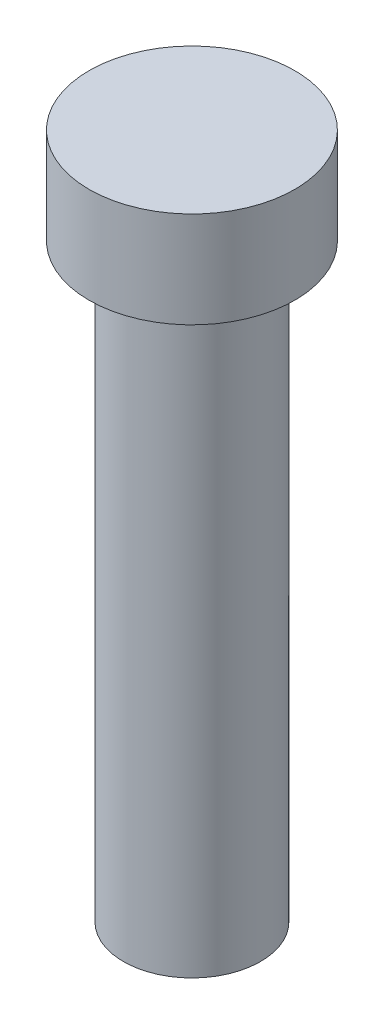
SolidWorks part; units mm, degrees
ref_plane "Front Plane" through (0, 0, 0) normal (0, 0, 1) x (1, 0, 0)
ref_plane "Top Plane" through (0, 0, 0) normal (0, 1, 0) x (1, 0, 0)
ref_plane "Right Plane" through (0, 0, 0) normal (1, 0, 0) x (0, 0, -1)
sketch "Sketch1" plane through (0, 0, 0) normal (0, 1, 0) x (1, 0, 0)
  circle A0 centre (0, 0) radius 7.5
  dimension "D1" = 15
extrude "Boss-Extrude1" add sketch "Sketch1" along normal blind 7
sketch "Sketch3" plane through (0, 0, 0) normal (0, -1, 0) x (1, 0, 0)
  circle A0 centre (0, 0) radius 5
  dimension "D1" = 10
extrude "Boss-Extrude2" add sketch "Sketch3" along normal blind 43
